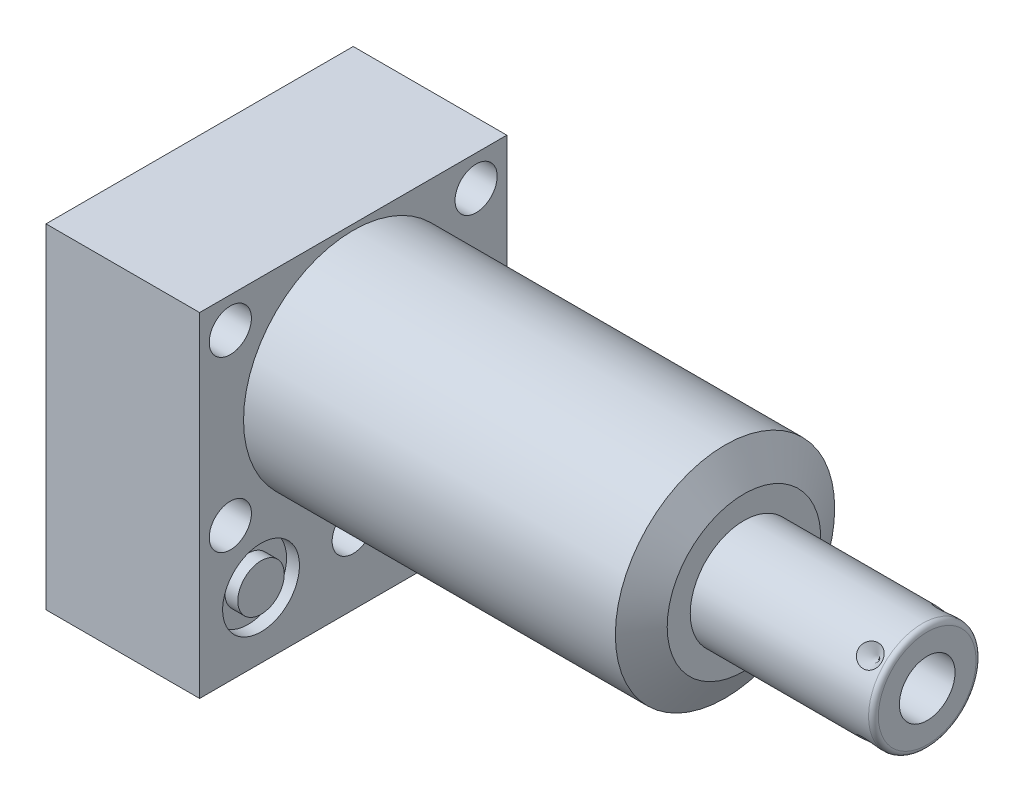
SolidWorks part; units mm, degrees
material "Alloy Steel"
ref_plane "Front Plane" through (0, 0, 0) normal (0, 0, 1) x (1, 0, 0)
ref_plane "Top Plane" through (0, 0, 0) normal (0, 1, 0) x (1, 0, 0)
ref_plane "Right Plane" through (0, 0, 0) normal (1, 0, 0) x (0, 0, -1)
ref_plane "Plane1" through (0, 0, 0) normal (1, 0, 0) x (0, 0, -1)
sketch "Sketch1" plane through (0, 0, 0) normal (1, 0, 0) x (0, 0, -1)
  line L0 (-31.75, 23.8252) -> (-31.75, -45.2628)
  line L1 (-31.75, -45.2628) -> (31.75, -45.2628)
  line L2 (31.75, -45.2628) -> (31.75, 23.8252)
  line L3 (31.75, 23.8252) -> (-31.75, 23.8252)
  line L4 (0, -55.6514) -> (0, 27.6098) construction
  dimension "D1" = 63.5
  dimension "D2" = 69.088
  dimension "D3" = 23.8252
extrude "Extrude1" add sketch "Sketch1" along normal blind 80.772 and the other way blind 31.75
ref_plane "Plane2" through (0, 0, 0) normal (1, 0, 0) x (0, 0, -1)
sketch "Sketch2" plane through (0, 0, 0) normal (1, 0, 0) x (0, 0, -1)
  line L0 (-26.0541, 0) -> (26.0541, 0) construction
  line L5 (31.75, 23.8252) -> (-31.75, 23.8252)
  line L6 (-31.75, 23.8252) -> (-31.75, -45.2628)
  line L7 (-31.75, -45.2628) -> (31.75, -45.2628)
  line L8 (31.75, -45.2628) -> (31.75, 23.8252)
  line L9 (31.75, 23.8252) -> (-31.75, 23.8252)
  line L10 (-31.75, 23.8252) -> (-31.75, -45.2628)
  line L11 (-31.75, -45.2628) -> (31.75, -45.2628)
  line L12 (31.75, -45.2628) -> (31.75, 23.8252)
  circle A0 centre (0, 0) radius 22.6695
  dimension "D1" = 45.339
  dimension "D2" = 0
extrude "Cut-Extrude1" cut sketch "Sketch2" along normal up to next
ref_plane "Plane3" through (0, 0, 0) normal (0, 0, 1) x (1, 0, 0)
sketch "Sketch3" plane through (0, 0, 0) normal (0, 0, 1) x (1, 0, 0)
  line L0 (76.8492, 22.6695) -> (80.772, 15.875)
  line L1 (76.0371, 0) -> (80.9975, 0) construction
  line L2 (80.772, 22.6695) -> (80.772, 15.875)
  line L3 (80.772, 22.6695) -> (76.8492, 22.6695)
  line L4 (80.772, 22.6695) -> (0, 22.6695) construction
  line L5 (80.772, -22.6695) -> (80.772, 22.6695) construction
  dimension "D1" = 31.75
  dimension "D2" = 30
revolve "Cut-Revolve1" cut sketch "Sketch3" angle 360 about L1
ref_plane "Plane4" through (-29.083, -31.75, 19.05) normal (0, 0, 1) x (0, 1, 0)
sketch "S2D0002" plane through (-29.083, -31.75, 19.05) normal (0, 0, 1) x (0, 1, 0)
  line L0 (0, 0) -> (4.5466, 0)
  line L1 (4.5466, 0) -> (4.1066, -2.0701)
  line L2 (4.1066, -2.0701) -> (3.4544, -2.7223)
  line L3 (3.4544, -2.7223) -> (3.4544, -13.97)
  line L4 (3.4544, -13.97) -> (0, -13.97)
  line L5 (0, -13.97) -> (0, 0)
  line L6 (0, -14.6685) -> (0, 0.6985) construction
  dimension "D1" = 13.97
revolve "Cut-Revolve2" cut sketch "S2D0002" angle 360 about L6
ref_plane "Plane5" through (-29.083, -31.75, -19.05) normal (0, 0, 1) x (0, 1, 0)
sketch "Sketch5" plane through (-29.083, -31.75, -19.05) normal (0, 0, 1) x (0, 1, 0)
  line L0 (0, 0) -> (4.5466, 0)
  line L1 (4.5466, 0) -> (4.1066, -2.0701)
  line L2 (4.1066, -2.0701) -> (3.4544, -2.7223)
  line L3 (3.4544, -2.7223) -> (3.4544, -13.97)
  line L4 (3.4544, -13.97) -> (0, -13.97)
  line L5 (0, -13.97) -> (0, 0)
  line L6 (0, -14.6685) -> (0, 0.6985) construction
  dimension "D1" = 13.97
revolve "Cut-Revolve3" cut sketch "Sketch5" angle 360 about L6
ref_plane "Plane6" through (-2.667, -31.75, 19.05) normal (0, 0, 1) x (0, -1, 0)
sketch "Sketch6" plane through (-2.667, -31.75, 19.05) normal (0, 0, 1) x (0, -1, 0)
  line L0 (0, 0) -> (4.5466, 0)
  line L1 (4.5466, 0) -> (4.1066, -2.0701)
  line L2 (4.1066, -2.0701) -> (3.4544, -2.7223)
  line L3 (3.4544, -2.7223) -> (3.4544, -12.192)
  line L4 (3.4544, -12.192) -> (0, -12.192)
  line L5 (0, -12.192) -> (0, 0)
  line L6 (0, -12.8016) -> (0, 0.6096) construction
  dimension "D1" = 12.192
revolve "Cut-Revolve4" cut sketch "Sketch6" angle 360 about L6
ref_plane "Plane7" through (-2.667, -31.75, -19.05) normal (0, 0, 1) x (0, -1, 0)
sketch "Sketch7" plane through (-2.667, -31.75, -19.05) normal (0, 0, 1) x (0, -1, 0)
  line L0 (0, 0) -> (4.5466, 0)
  line L1 (4.5466, 0) -> (4.1066, -2.0701)
  line L2 (4.1066, -2.0701) -> (3.4544, -2.7223)
  line L3 (3.4544, -2.7223) -> (3.4544, -12.192)
  line L4 (3.4544, -12.192) -> (0, -12.192)
  line L5 (0, -12.192) -> (0, 0)
  line L6 (0, -12.8016) -> (0, 0.6096) construction
  dimension "D1" = 12.192
revolve "Cut-Revolve5" cut sketch "Sketch7" angle 360 about L6
ref_plane "Plane8" through (-15.875, -51.6128, 19.05) normal (0, 0, 1) x (-1, 0, 0)
sketch "Sketch8" plane through (-15.875, -51.6128, 19.05) normal (0, 0, 1) x (-1, 0, 0)
  line L0 (0, -6.604) -> (6.1849, -6.604)
  line L1 (6.1849, -6.604) -> (5.6423, -9.1567)
  line L2 (5.6423, -9.1567) -> (4.9784, -9.8206)
  line L3 (4.9784, -9.8206) -> (4.9784, -25.654)
  line L4 (4.9784, -25.654) -> (0, -25.654)
  line L5 (0, -25.654) -> (0, -6.604)
  line L6 (0, -26.67) -> (0, 1.27) construction
  line L7 (15.875, -6.35) -> (-15.875, -6.35) construction
  dimension "D1" = 19.05
  dimension "D2" = 0.254
revolve "Cut-Revolve6" cut sketch "Sketch8" angle 360 about L6
ref_plane "Plane9" through (-15.875, -51.6128, -19.05) normal (0, 0, 1) x (-1, 0, 0)
sketch "Sketch9" plane through (-15.875, -51.6128, -19.05) normal (0, 0, 1) x (-1, 0, 0)
  line L0 (0, -6.604) -> (6.1849, -6.604)
  line L1 (6.1849, -6.604) -> (5.6423, -9.1567)
  line L2 (5.6423, -9.1567) -> (4.9784, -9.8206)
  line L3 (4.9784, -9.8206) -> (4.9784, -25.654)
  line L4 (4.9784, -25.654) -> (0, -25.654)
  line L5 (0, -25.654) -> (0, -6.604)
  line L6 (0, -26.67) -> (0, 1.27) construction
  line L7 (15.875, -6.35) -> (-15.875, -6.35) construction
  dimension "D1" = 19.05
  dimension "D2" = 0.254
revolve "Cut-Revolve7" cut sketch "Sketch9" angle 360 about L6
ref_plane "Plane10" through (0, 0, 0) normal (0, 0, 1) x (1, 0, 0)
sketch "Sketch18" plane through (0, 0, 0) normal (1, 0, 0) x (0, 0, -1)
  circle A0 centre (-19.05, -31.75) radius 7.9375
  circle A1 centre (19.05, -31.75) radius 7.9375
  dimension "D1" = 15.875
extrude "Cut-Extrude2" cut sketch "Sketch18" against normal blind 2.667
sketch "Sketch19" plane through (-31.75, 0, 0) normal (-1, 0, 0) x (0, 0, 1)
  circle A0 centre (-19.05, -31.75) radius 7.9375
  circle A1 centre (19.05, -31.75) radius 7.9375
  dimension "D1" = 15.875
extrude "Cut-Extrude3" cut sketch "Sketch19" against normal blind 2.667
sketch "Sketch20" plane through (0, -45.2628, 0) normal (0, -1, 0) x (1, 0, 0)
  circle A0 centre (-15.875, -19.05) radius 9.525
  circle A1 centre (-15.875, 19.05) radius 9.525
  circle A2 centre (-15.875, 19.05) radius 6.1849 construction
  dimension "D1" = 19.05
extrude "Cut-Extrude4" cut sketch "Sketch20" against normal blind 0.254
sketch "Sketch10" plane through (0, 0, 0) normal (0, 0, 1) x (1, 0, 0)
  line L0 (80.772, 0) -> (80.772, 11.1125)
  line L1 (80.772, 11.1125) -> (117.6274, 11.1125)
  line L2 (118.6434, 10.0965) -> (118.6434, 0)
  line L3 (118.6434, 0) -> (80.772, 0)
  line L4 (58.2708, 0) -> (120.537, 0) construction
  line L5 (80.772, -15.875) -> (80.772, 15.875) construction
  line L6 (-31.75, 23.8252) -> (-31.75, -45.2628) construction
  arc A0 (118.6434, 10.0965) -> (117.6274, 11.1125) centre (117.6274, 10.0965) ccw
  point P0 (80.772, 0)
  dimension "D2" = 1.016
  dimension "D1" = 22.225
  dimension "D3" = 150.3934
revolve "Revolve1" add sketch "Sketch10" angle 360 about L4
ref_plane "Plane11" through (118.6434, -5.7531, 0) normal (0, 0, 1) x (0, -1, 0)
sketch "S2D0001" plane through (118.6434, -5.7531, 0) normal (0, 0, 1) x (0, -1, 0)
  line L0 (0, 0) -> (0, -17.018)
  line L1 (0, -17.018) -> (-5.7531, -20.4748)
  line L2 (0, 0) -> (-5.7531, 0)
  line L3 (-5.7531, 0) -> (-5.7531, -20.4748)
  line L4 (-5.7531, -34.3471) -> (-5.7531, 1.0237) construction
  line L5 (4.3434, 0) -> (-15.8496, 0) construction
  dimension "D1" = 11.5062
  dimension "D2" = 17.018
  dimension "D3" = 59
revolve "Cut-Revolve8" cut sketch "S2D0001" angle 360 about L4
ref_plane "Plane12" through (-31.75, -51.6128, 0) normal (0, -1, 0) x (0, 0, -1)
sketch "Sketch12" plane through (-31.75, -45.0088, 0) normal (0, -1, 0) x (0, 0, -1)
  circle A0 centre (-19.05, 15.875) radius 6.4389
  circle A1 centre (-19.05, 15.875) radius 9.525 construction
  dimension "D1" = 12.8778
extrude "Extrude2" add sketch "Sketch12" along normal blind 1.651
sketch "Sketch13" plane through (0, 0, 0) normal (1, 0, 0) x (0, 0, -1)
  circle A0 centre (-19.05, -31.75) radius 4.8006
  circle A1 centre (-19.05, -31.75) radius 7.9375 construction
  dimension "D1" = 9.6012
ref_plane "Plane13" through (-31.75, 0, 0) normal (1, 0, 0) x (0, 0, -1)
extrude "Extrude3" add sketch "Sketch13" along normal up to surface
ref_plane "Plane14" through (0, -31.75, -19.05) normal (0, -1, 0) x (0, 0, -1)
sketch "Sketch14" plane through (0, -31.75, -19.05) normal (0, -1, 0) x (0, 0, -1)
  line L0 (0, -2.8435) -> (0, 1.0401) construction
  line L1 (0, -5.3893) -> (0, -12.2901) construction
  line L2 (7.9375, -2.667) -> (-7.9375, -2.667) construction
  circle A0 centre (6.1722, -0.9017) radius 1.7653
  dimension "D1" = 3.5306
  dimension "D2" = 12.3444
revolve "Revolve2" add sketch "Sketch14" angle 360 about L0
ref_plane "Plane15" through (0, -31.75, -19.05) normal (0, -1, 0) x (0, 0, -1)
sketch "Sketch15" plane through (0, -31.75, -19.05) normal (0, -1, 0) x (0, 0, -1)
  line L0 (0, -32.7901) -> (0, -28.9065) construction
  line L1 (0, -29.083) -> (0, -27.0129) construction
  line L2 (-7.9375, -29.083) -> (7.9375, -29.083) construction
  circle A0 centre (6.1722, -30.8483) radius 1.7653
  dimension "D1" = 3.5306
  dimension "D2" = 12.3444
revolve "Revolve3" add sketch "Sketch15" angle 360 about L0
ref_plane "Plane18" through (0, 0, 0) normal (0, 0.7071, 0.7071) x (-1, 0, 0)
ref_plane "Plane16" through (114.681, -11.1125, 0) normal (0, 0, 1) x (-1, 0, 0)
sketch "Sketch16" plane through (114.681, 7.8577, -7.8577) normal (0, -0.7071, -0.7071) x (-1, 0, 0)
  line L0 (0, 0) -> (2.413, 0)
  line L1 (2.413, 0) -> (0, -2.413)
  line L2 (0, 0) -> (0, -2.413)
  line L3 (0, -5.0193) -> (0, 0.1207) construction
  line L4 (33.909, 0) -> (-2.9464, 0) construction
  line L5 (-3.9624, -1.016) -> (-3.9624, -21.209) construction
  dimension "D1" = 3.9624
  dimension "D2" = 4.826
  dimension "D3" = 45
ref_plane "Plane17" through (114.681, 11.1125, 0) normal (0, 0, 1) x (1, 0, 0)
revolve "Cut-Revolve9" cut sketch "Sketch16" angle 360 about L3
pattern_circular "CirPattern1" count 4 over 360 of "Cut-Revolve9"
hole_wizard "Hole1" positions "Sketch22" profile "Sketch21" legacy end condition up to next
sketch "Sketch22" plane through (0, 0, 0) normal (1, 0, 0) x (0, 0, -1)
  line L0 (0, 0) -> (-38.8053, 0) construction
  line L1 (0, 0) -> (0, 31.2017) construction
  point P0 (-25.4, 17.4752)
  point P1 (0, -30.8356)
  point P12 (-25.4, -17.4752)
  point P14 (25.4, 17.4752)
  point P15 (25.4, -17.4752)
  dimension "D1" = 25.4
  dimension "D2" = 17.4752
  dimension "D3" = 30.8356
sketch "Sketch21" plane through (0, 17.4752, 25.4) normal (0, 1, 0) x (0, 0, -1)
  line L0 (0, 0) -> (0, 31.75)
  line L1 (0, 31.75) -> (4.3561, 31.75)
  line L2 (4.3561, 31.75) -> (4.3561, 0)
  line L3 (4.3561, 0) -> (0, 0)
  line L4 (0, 110) -> (0, -10) construction
  dimension "Diameter" = 8.7122
  dimension "Depth" = 31.75
